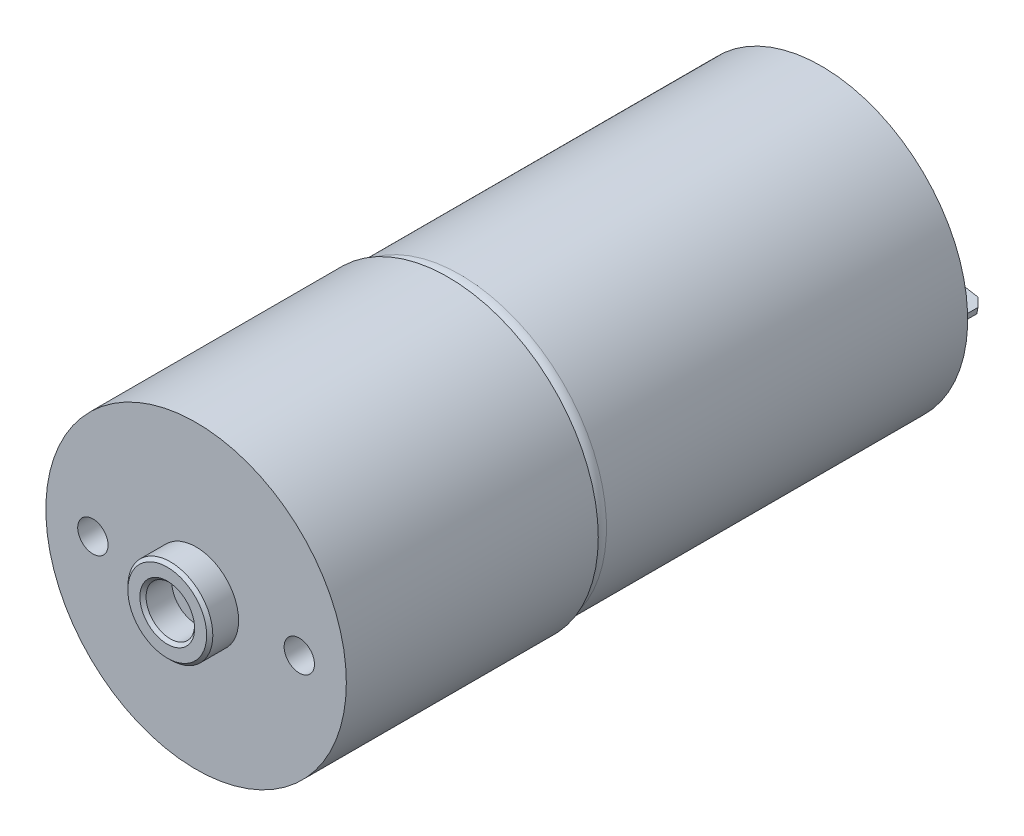
SolidWorks part; units mm, degrees
ref_plane "Front" through (0, 0, 0) normal (0, 0, 1) x (1, 0, 0)
ref_plane "Top" through (0, 0, 0) normal (0, 1, 0) x (1, 0, 0)
ref_plane "Right" through (0, 0, 0) normal (1, 0, 0) x (0, 0, -1)
sketch "Sketch1" plane through (0, 0, 0) normal (0, 0, 1) x (1, 0, 0)
  circle A1 centre (0, 0) radius 12.05
  dimension "D1" = 24.1
extrude "Boss-Extrude1" add sketch "Sketch1" along normal blind 30.75
fillet "Fillet2" radius 1 1 edges at (-12.05, 0, 30.75)
sketch "Sketch2" plane through (0, 0, 30.75) normal (0, 0, 1) x (1, 0, 0)
  circle A0 centre (0, 0) radius 12.375
  dimension "D1" = 24.75
extrude "Boss-Extrude2" add sketch "Sketch2" along normal blind 20.75
sketch "Sketch3" plane through (0, 0, 51.5) normal (0, 0, 1) x (1, 0, 0)
  circle A0 centre (0, 0) radius 3.5
  circle A1 centre (0, 0) radius 2
  dimension "D1" = 7
  dimension "D2" = 4
extrude "Boss-Extrude3" add sketch "Sketch3" along normal blind 2.375
chamfer "Chamfer1" distance 0.254 angle 45 2 edges at (2, 0, 53.875) (3.5, 0, 53.875)
hole_wizard "M3x0.5 Tapped Hole1" positions "Sketch5" profile "Sketch6" tap size "M3x0.5" standard "ANSI Metric"
sketch "Sketch5" plane through (0, 0, 51.5) normal (0, 0, 1) x (1, 0, 0)
  line L0 (-8.5, 0) -> (8.5, 0) construction
  point P0 (-8.5, 0)
  point P2 (8.5, 0)
  dimension "D1" = 17
sketch "Sketch6" plane through (-8.5, 0, 51.5) normal (1, 0, 0) x (0, -1, 0)
  line L0 (0, 0) -> (0, 8.2511)
  line L1 (0, 8.2511) -> (1.25, 7.5)
  line L2 (1.25, 7.5) -> (1.25, 0)
  line L5 (1.25, 0) -> (0, 0)
  line L10 (0, 8.2511) -> (-1.25, 7.5) construction
  line L11 (0, -6.35) -> (0, 107.95) construction
  dimension "Tap Drill Dia." = 2.5
  dimension "Tap Drill Depth" = 7.5
  dimension "Drill Angle" = 118
cosmetic thread "Hole Thread1" parameters "D1"=6, "D2"=3
cosmetic thread "Hole Thread2" parameters "D1"=6, "D2"=3
sketch "Sketch7" plane through (0, 0, 0) normal (0, 0, -1) x (-1, 0, 0)
  circle A0 centre (0, 0) radius 11.8
  circle A15 centre (0, 0) radius 12.05
  circle A17 centre (0, 0) radius 12.05 construction
  dimension "D1" = 0
  dimension "D2" = 0.25
extrude "Cut-Extrude1" cut sketch "Sketch7" against normal blind 0.762
sketch "Sketch8" plane through (0, 0, 0.762) normal (0, 0, -1) x (-1, 0, 0)
  circle A0 centre (0, 0) radius 4.5
  dimension "D1" = 9
extrude "Boss-Extrude4" add sketch "Sketch8" along normal blind 0.254 draft 60
sketch "Sketch9" plane through (0, 0, 0.508) normal (0, 0, -1) x (-1, 0, 0)
  circle A0 centre (0, 0) radius 3.1875
  dimension "D1" = 6.375
extrude "Boss-Extrude5" add sketch "Sketch9" along normal blind 2.413
fillet "Fillet1" radius 0.254 2 edges at (-3.1875, 0, 0.508) (-3.1875, 0, -1.905)
sketch "Sketch10" plane through (0, 0, 0.762) normal (0, 0, -1) x (-1, 0, 0)
  line L0 (8.8633, 1.5628) -> (-8.8633, -1.5628) construction
  line L1 (0, 0) -> (9.8425, 0) construction
  circle A1 centre (8.8633, 1.5628) radius 1.524
  circle A2 centre (-8.8633, -1.5628) radius 1.524
  dimension "D3" = 3.048
  dimension "D1" = 10
  dimension "D2" = 18
extrude "Boss-Extrude6" add sketch "Sketch10" along normal blind 1.016
sketch "Sketch11" plane through (0, 0, -0.254) normal (0, 0, -1) x (-1, 0, 0)
  line L0 (8.8633, 1.5628) -> (-8.8633, -1.5628) construction
  line L2 (-10.0073, -2.0225) -> (-7.631, -1.6035)
  line L3 (-10.0073, -2.0225) -> (-10.0955, -1.5222)
  line L4 (-10.0955, -1.5222) -> (-7.7192, -1.1032)
  line L5 (-7.631, -1.6035) -> (-7.7192, -1.1032)
  line L6 (-10.0073, -2.0225) -> (-7.7192, -1.1032) construction
  line L7 (-10.0955, -1.5222) -> (-7.631, -1.6035) construction
  line L8 (7.7192, 1.1032) -> (10.0955, 1.5222)
  line L9 (7.7192, 1.1032) -> (7.631, 1.6035)
  line L10 (7.631, 1.6035) -> (10.0073, 2.0225)
  line L11 (10.0955, 1.5222) -> (10.0073, 2.0225)
  line L12 (7.7192, 1.1032) -> (10.0073, 2.0225) construction
  line L13 (7.631, 1.6035) -> (10.0955, 1.5222) construction
  circle A0 centre (-8.8633, -1.5628) radius 1.524 construction
  dimension "D1" = 2.413
  dimension "D2" = 0.508
  dimension "D3" = 0.508
  dimension "D4" = 2.413
extrude "Boss-Extrude7" add sketch "Sketch11" along normal blind 3.175 contours L10 L11 L8 L9 | L2 L5 L4 L3
sketch "Sketch12" plane through (0.0441, 0.2501, 0) normal (0.1736, 0.9848, 0) x (0.9848, -0.1736, 0)
  line L0 (-9, 3.429) -> (-9, 0.254) construction
  line L1 (-7.7935, 3.429) -> (-10.2065, 3.429) construction
  line L2 (-7.7935, 0.254) -> (-10.2065, 0.254) construction
  line L3 (9, 3.429) -> (9, 0.254) construction
  line L4 (10.2065, 3.429) -> (7.7935, 3.429) construction
  line L5 (10.524, 0.254) -> (7.476, 0.254) construction
  circle A0 centre (-9, 2.159) radius 0.635
  circle A1 centre (9, 2.159) radius 0.635
  dimension "D1" = 1.27
  dimension "D2" = 1.905
extrude "Cut-Extrude2" cut sketch "Sketch12" against normal blind 3.175
chamfer "Chamfer2" distance 0.635 angle 45 4 edges at (10.0514, -1.7723, -3.429) (7.6751, -1.3533, -3.429) (-10.0514, 1.7723, -3.429) (-7.6751, 1.3533, -3.429)
sketch "Sketch13" plane through (0, 0, 0.762) normal (0, 0, -1) x (-1, 0, 0)
  line L0 (-8.8633, 2) -> (-8.8633, -2) construction
  line L1 (-7.3393, 2) -> (-7.3393, -2)
  line L2 (-10.3873, 2) -> (-10.3873, -2)
  line L3 (0, 0) -> (0, -11.8) construction
  line L4 (8.8633, 2) -> (8.8633, -2) construction
  line L5 (7.3393, 2) -> (7.3393, -2)
  line L6 (10.3873, 2) -> (10.3873, -2)
  arc A0 (-7.3393, 2) -> (-10.3873, 2) centre (-8.8633, 2) ccw
  arc A1 (-10.3873, -2) -> (-7.3393, -2) centre (-8.8633, -2) ccw
  circle A2 centre (-8.8633, -1.5628) radius 1.524 construction
  circle A3 centre (-8.8633, -1.5628) radius 1.524 construction
  circle A5 centre (0, 0) radius 11.8 construction
  arc A6 (7.3393, 2) -> (10.3873, 2) centre (8.8633, 2) cw
  arc A7 (10.3873, -2) -> (7.3393, -2) centre (8.8633, -2) cw
  point P2 (-8.8633, 0)
  point P7 (-8.8633, -1.5628)
  point P21 (8.8633, 0)
  point P26 (8.8633, -1.5628)
  dimension "D1" = 4
extrude "Boss-Extrude8" add sketch "Sketch13" along normal up to surface (1.016 mm away) up to face at (-8.8633, 1.5628, -0.254)
sketch "Sketch14" plane through (0, 0, 0.762) normal (0, 0, -1) x (-1, 0, 0)
  line L0 (4.1136, 2.375) -> (-4.1136, -2.375) construction
  line L1 (0, 0) -> (2.9335, 0) construction
  line L2 (4.1136, -2.375) -> (-4.1136, 2.375) construction
  circle A2 centre (0, 0) radius 4.75
  arc A3 (-4.1136, 2.375) -> (-4.1136, -2.375) centre (0, 0) ccw
  circle A4 centre (0, 0) radius 2.9335 construction
  circle A5 centre (0, 0) radius 4.25
  arc A6 (-3.6806, 2.125) -> (-3.6806, -2.125) centre (0, 0) ccw
  arc A7 (4.1136, -2.375) -> (4.1136, 2.375) centre (0, 0) ccw
  arc A8 (3.6806, -2.125) -> (3.6806, 2.125) centre (0, 0) ccw
  arc A9 (4.1136, 2.375) -> (3.6806, 2.125) centre (3.8971, 2.25) ccw
  arc A10 (3.6806, -2.125) -> (4.1136, -2.375) centre (3.8971, -2.25) ccw
  arc A11 (-3.6806, -2.125) -> (-4.1136, -2.375) centre (-3.8971, -2.25) cw
  arc A12 (-4.1136, 2.375) -> (-3.6806, 2.125) centre (-3.8971, 2.25) cw
  dimension "D3" = 60
  dimension "D4" = 30
  dimension "D1" = 0.25
  dimension "D2" = 0.25
extrude "Cut-Extrude3" cut sketch "Sketch14" against normal blind 3 and the other way blind 10
sketch "Sketch15" plane through (0, 0, 0.762) normal (0, 0, -1) x (-1, 0, 0)
  line L0 (-8.1915, 5.7358) -> (8.1915, -5.7358) construction
  line L1 (0, 0) -> (0, -11.8) construction
  line L2 (8.1915, 5.7358) -> (-8.1915, -5.7358) construction
  circle A0 centre (0, 0) radius 11.8 construction
  circle A1 centre (-8.1915, 5.7358) radius 1
  circle A2 centre (8.1915, 5.7358) radius 1
  circle A3 centre (8.1915, -5.7358) radius 1
  circle A4 centre (-8.1915, -5.7358) radius 1
  dimension "D4" = 2
  dimension "D1" = 20
  dimension "D2" = 55
  dimension "D3" = 55
extrude "Boss-Extrude9" add sketch "Sketch15" along normal blind 0.5
